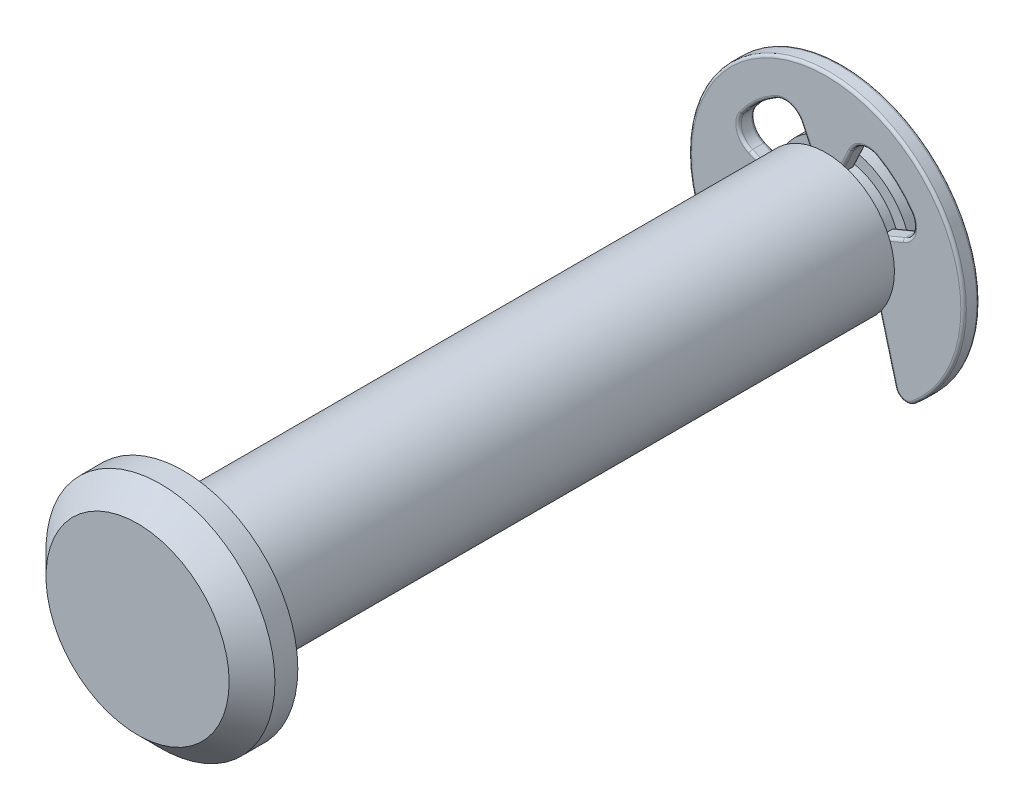
SolidWorks part; units mm, degrees
material "Plain Carbon Steel"
ref_plane "Front Plane" through (0, 0, 0) normal (0, 0, 1) x (1, 0, 0)
ref_plane "Top Plane" through (0, 0, 0) normal (0, 1, 0) x (1, 0, 0)
ref_plane "Right Plane" through (0, 0, 0) normal (1, 0, 0) x (0, 0, -1)
sketch "Sketch1" plane through (0, 0, 0) normal (1, 0, 0) x (0, 0, -1)
  line L0 (-15, 0) -> (15, 0) construction
  line L1 (-15, 0) -> (-17, 0) construction
  line L2 (-17, 0) -> (-17, 4)
  line L3 (-17, 4) -> (-16, 5)
  line L4 (-16, 5) -> (-15, 5)
  line L5 (-15, 5) -> (-15, 3)
  line L6 (-15, 3) -> (13.06, 3)
  line L7 (13.06, 3) -> (13.06, 2.5)
  line L8 (13.06, 2.5) -> (13.8, 2.5)
  line L9 (13.8, 2.5) -> (13.8, 3)
  line L10 (13.8, 3) -> (15, 3)
  line L11 (15, 3) -> (15, 0)
  line L12 (13.43, 2.5) -> (13.43, 3) construction
  line L13 (13.08, 0) -> (13.08, 6)
  line L14 (13.08, 6) -> (13.78, 6)
  line L15 (13.78, 6) -> (13.78, 0)
  dimension "Length" = 30
  dimension "Head Height" = 2
  dimension "D1" = 45
  dimension "Head Chamfer Length" = 1
  dimension "Groove Dia" = 5
  dimension "Dia" = 6
  dimension "Head Dia" = 10
  dimension "Ring Dia" = 12
  dimension "Ring Thickness" = 0.7
sketch "Sketch2" plane through (0, 0, 0) normal (1, 0, 0) x (0, 0, -1)
  line L0 (15, 3) -> (15, 0) construction
  line L1 (13.8, 3) -> (15, 3) construction
  line L2 (13.8, 2.5) -> (13.8, 3) construction
  line L3 (13.06, 2.5) -> (13.8, 2.5) construction
  line L4 (13.06, 3) -> (13.06, 2.5) construction
  line L5 (-15, 3) -> (13.06, 3) construction
  line L6 (-15, 5) -> (-15, 3) construction
  line L7 (-16, 5) -> (-15, 5) construction
  line L8 (-17, 4) -> (-16, 5) construction
  line L9 (-17, 0) -> (-17, 4) construction
  line L10 (15, 3) -> (15, 0)
  line L11 (13.8, 3) -> (15, 3)
  line L12 (13.8, 2.5) -> (13.8, 3)
  line L13 (13.06, 2.5) -> (13.8, 2.5)
  line L14 (13.06, 3) -> (13.06, 2.5)
  line L15 (-15, 3) -> (13.06, 3)
  line L16 (-15, 5) -> (-15, 3)
  line L17 (-16, 5) -> (-15, 5)
  line L18 (-17, 4) -> (-16, 5)
  line L19 (-17, 0) -> (-17, 4)
  line L20 (-17, 0) -> (15, 0)
revolve "Revolve1" add sketch "Sketch2" angle 360 about L0
ref_plane "Plane1" through (0, 0, -13.43) normal (0, 0, -1) x (-1, 0, 0)
sketch "Sketch3" plane through (0, 0, -13.43) normal (0, 0, -1) x (-1, 0, 0)
  line L6 (-1.0931, 3.5605) -> (-0.5681, 2.4346)
  line L7 (0.5681, 2.4346) -> (1.0931, 3.5605)
  line L8 (3.3375, 1.3824) -> (2.3097, 0.9567)
  line L9 (2.1614, -1.2563) -> (3, -4.386)
  line L10 (-3, -4.386) -> (-2.1614, -1.2563)
  line L11 (-2.3097, 0.9567) -> (-3.3375, 1.3824)
  line L12 (0, 0) -> (0, 4.5) construction
  line L13 (0, 0) -> (4.5, 0) construction
  arc A15 (-2.2113, 3.9192) -> (-3.6868, 2.5803) centre (0, 0) ccw
  arc A16 (-1.0931, 3.5605) -> (-2.2113, 3.9192) centre (-1.8182, 3.2225) ccw
  arc A19 (2.2113, 3.9192) -> (1.0931, 3.5605) centre (1.8182, 3.2225) ccw
  arc A20 (3.6868, 2.5803) -> (2.2113, 3.9192) centre (0, 0) ccw
  arc A21 (3.3375, 1.3824) -> (3.6868, 2.5803) centre (3.0313, 2.1215) ccw
  arc A22 (2.1614, -1.2563) -> (2.3097, 0.9567) centre (0, 0) ccw
  arc A23 (3, -4.386) -> (3.7996, -4.6436) centre (3.483, -4.2566) ccw
  arc A26 (-3.7996, -4.6436) -> (-3, -4.386) centre (-3.483, -4.2566) ccw
  arc A27 (-2.3097, 0.9567) -> (-2.1614, -1.2563) centre (0, 0) ccw
  arc A28 (-3.6868, 2.5803) -> (-3.3375, 1.3824) centre (-3.0313, 2.1215) ccw
  circle A30 centre (0, 0) radius 2.5
  circle A31 centre (0, 0) radius 6
  circle A32 centre (0, 0) radius 4.5 construction
  dimension "D1" = 9
  dimension "D6" = 0.5
  dimension "D7" = 0.8
  dimension "D2" = 30
  dimension "D3" = 50
  dimension "D4" = 97.5
  dimension "D8" = 97.5
  dimension "D5" = 6
  dimension "D9" = 3.6364
extrude "Boss-Extrude1" add sketch "Sketch3" along normal up to vertex (0.35 mm away) and the other way up to vertex (0.35 mm away) separate body contours A23 A31 A26 L10 A27 L11 A28 A15 A16 L6 A30 L7 A19 A20 A21 L8 A22 L9 up to point (0, 6, -13.78) other way up to point (0, 6, -13.08)
fillet "Fillet1" radius 0.12 36 edges at (0, 6, -13.08) (3.3297, -4.7326, -13.08) (2.5807, -2.8212, -13.08) (2.4944, -0.1672, -13.08) (2.8236, 1.1696, -13.08) (3.7994, 1.8976, -13.08) (3.0241, 3.3324, -13.08) (1.5738, 3.9842, -13.08) (0.8306, 2.9976, -13.08) (0, 2.5, -13.08) (-0.8306, 2.9976, -13.08) (-1.5738, 3.9842, -13.08) (-3.0241, 3.3324, -13.08) (-3.7994, 1.8976, -13.08) (-2.8236, 1.1696, -13.08) (-2.4944, -0.1672, -13.08) (-2.5807, -2.8212, -13.08) (-3.3297, -4.7326, -13.08) (-2.5807, -2.8212, -13.78) (-2.4944, -0.1672, -13.78) (-2.8236, 1.1696, -13.78) (-3.7994, 1.8976, -13.78) (-3.0241, 3.3324, -13.78) (-1.5738, 3.9842, -13.78) (-0.8306, 2.9976, -13.78) (0, 2.5, -13.78) (0.8306, 2.9976, -13.78) (1.5738, 3.9842, -13.78) (3.0241, 3.3324, -13.78) (3.7994, 1.8976, -13.78) (2.8236, 1.1696, -13.78) (2.4944, -0.1672, -13.78) (2.5807, -2.8212, -13.78) (3.3297, -4.7326, -13.78) (0, 6, -13.78) (-3.3297, -4.7326, -13.78)
chamfer "Chamfer1" distance 0.6 angle 45 1 edges at (3, 0, -15)
equation "\"D1@Sketch3\"=\"Ring Dia@Sketch1\"*.75"
equation "\"D6@Sketch3\" = \"Ring Dia@Sketch1\" / 24"
equation "\"D7@Sketch3\" = \"Ring Dia@Sketch1\" / 15"
equation "\"D5@Sketch3\" = \"Ring Dia@Sketch1\" / 2"
equation "\"D9@Sketch3\"= \"Ring Dia@Sketch1\" / 3.3"
equation "\"D1@Fillet1\"=\"Ring Dia@Sketch1\"*.01"
equation "\"D1@Chamfer1\"=\"Dia@Sketch1\"/10"
